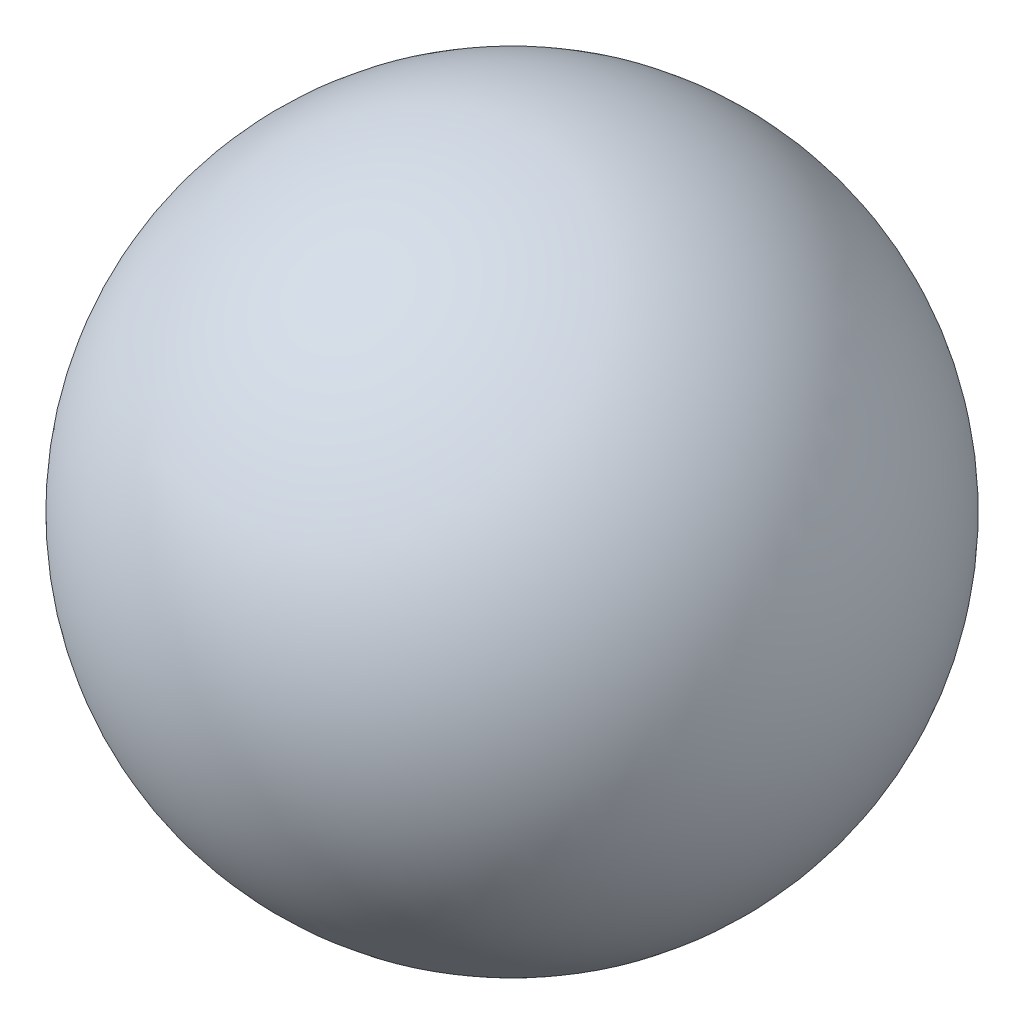
SolidWorks part; units mm, degrees
ref_plane "Ön Düzlem" through (0, 0, 0) normal (0, 0, 1) x (1, 0, 0)
ref_plane "Üst Düzlem" through (0, 0, 0) normal (0, 1, 0) x (1, 0, 0)
ref_plane "Sağ Düzlem" through (0, 0, 0) normal (1, 0, 0) x (0, 0, -1)
sketch "Sketch1" plane through (0, 0, 0) normal (0, 0, 1) x (1, 0, 0)
  line L0 (0, 1.65) -> (0, -1.65)
  arc A0 (0, 1.65) -> (0, -1.65) centre (0, 0) ccw
revolve "Revolve2" add sketch "Sketch1" angle 360 about L0
